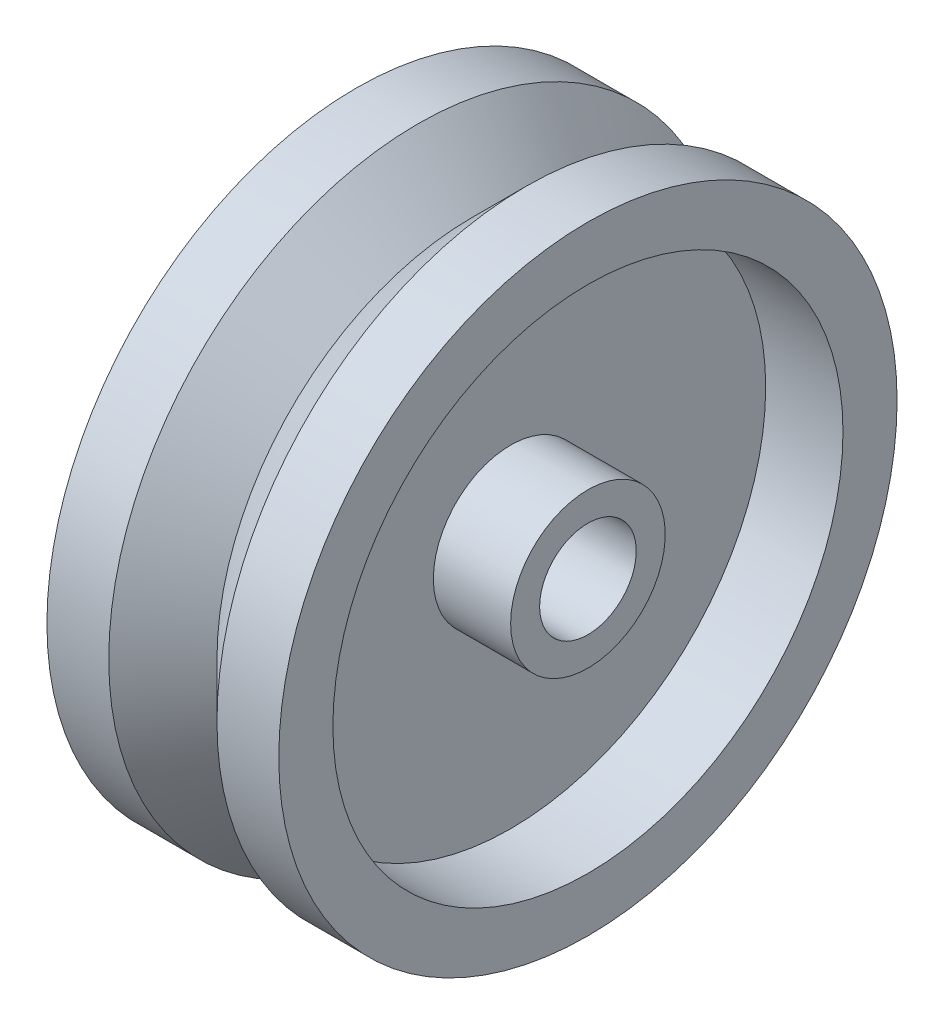
SolidWorks part; units mm, degrees
ref_plane "Front Plane" through (0, 0, 0) normal (0, 0, 1) x (1, 0, 0)
ref_plane "Top Plane" through (0, 0, 0) normal (0, 1, 0) x (1, 0, 0)
ref_plane "Right Plane" through (0, 0, 0) normal (1, 0, 0) x (0, 0, -1)
sketch "Sketch2" plane through (0, 0, 0) normal (0, 1, 0) x (1, 0, 0)
  line L0 (-0.8385, -3.3502) -> (15, -3.3502) construction
  line L1 (0, -6.4752) -> (15, -6.4752)
  line L5 (0, -6.4752) -> (0, -8.3502)
  line L6 (15, -6.4752) -> (15, -8.3502)
  line L7 (0, -19.8502) -> (0, -23.3502)
  line L8 (15, -19.8502) -> (15, -23.3502)
  line L9 (0, -8.3502) -> (5, -8.3502)
  line L10 (7.5, -19.8502) -> (4, -23.3502)
  line L11 (10, -8.3502) -> (10, -19.8502)
  line L12 (7.5, -19.8502) -> (11, -23.3502)
  line L13 (5, -8.3502) -> (5, -19.8502)
  line L14 (0, -23.3502) -> (4, -23.3502)
  line L15 (10, -8.3502) -> (15, -8.3502)
  line L18 (15, -23.3502) -> (11, -23.3502)
  line L19 (0, -19.8502) -> (5, -19.8502)
  line L20 (10, -19.8502) -> (15, -19.8502)
  dimension "D1" = 90
revolve "Revolve1" add sketch "Sketch2" angle 360 about L0
